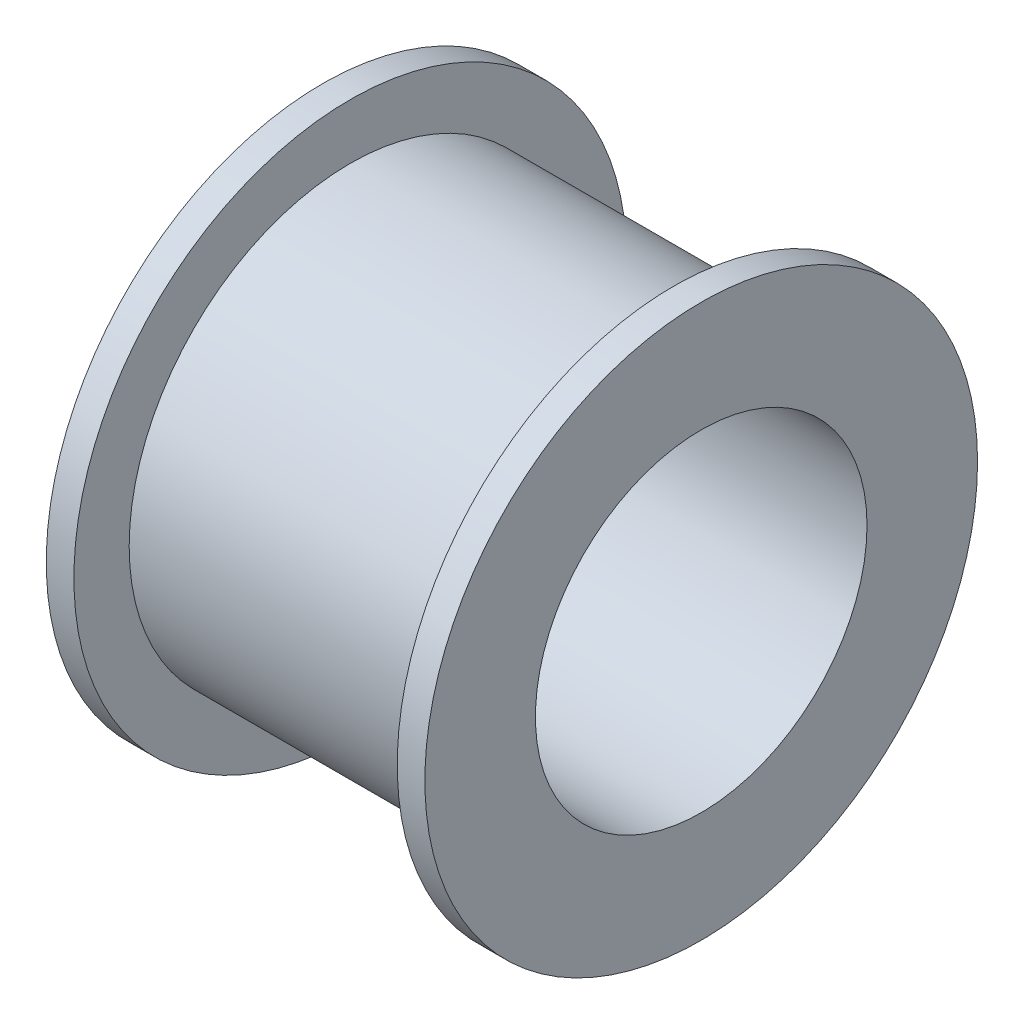
SolidWorks part; units mm, degrees
ref_plane "Front Plane" through (0, 0, 0) normal (0, 0, 1) x (1, 0, 0)
ref_plane "Top Plane" through (0, 0, 0) normal (0, 1, 0) x (1, 0, 0)
ref_plane "Right Plane" through (0, 0, 0) normal (1, 0, 0) x (0, 0, -1)
sketch "Sketch1" plane through (0, 0, 0) normal (0, 0, 1) x (1, 0, 0)
  line L0 (0, 100) -> (0, 60)
  line L1 (0, 100) -> (10, 100)
  line L2 (10, 100) -> (10, 80)
  line L3 (10, 80) -> (68.5, 80)
  line L4 (68.5, 80) -> (68.5, 60)
  line L5 (68.5, 60) -> (0, 60)
  dimension "D1" = 100
  dimension "D2" = 10
  dimension "D3" = 68.5
  dimension "D4" = 80
  dimension "D5" = 60
ref_axis "Axis1" through (71.925, 0, 0) along (-1, 0, 0)
revolve "Revolve1" add sketch "Sketch1" angle 360 about axis through (71.925, 0, 0) along (-1, 0, 0)
mirror "Mirror1" about plane through (68.5, 80, 0) normal (1, 0, 0) of "Revolve1"
